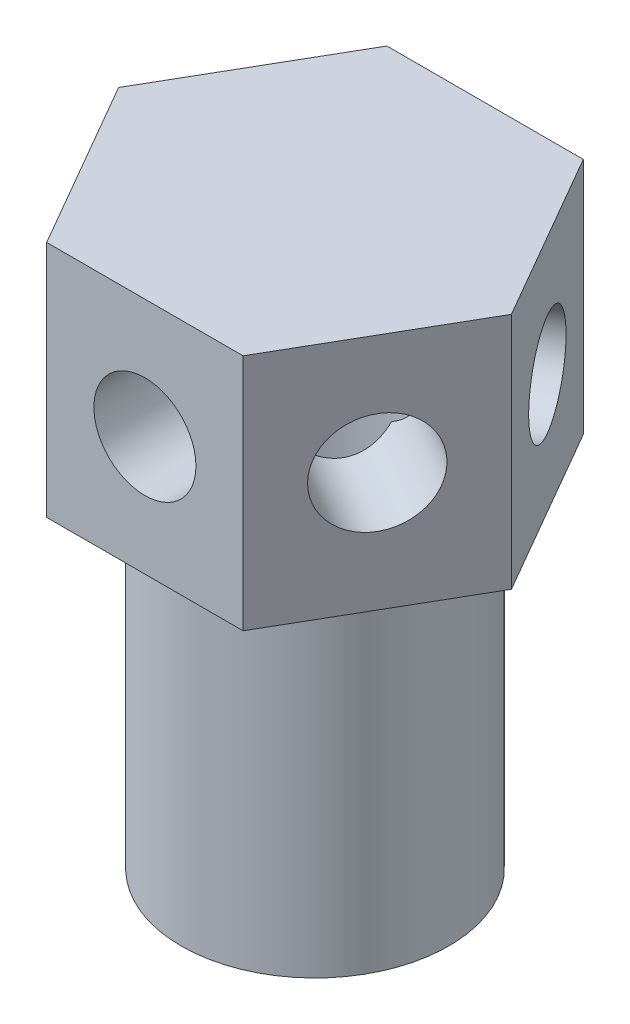
SolidWorks part; units mm, degrees
material "6063-T6"
ref_plane "Ebene vorne" through (0, 0, 0) normal (0, 0, 1) x (1, 0, 0)
ref_plane "Ebene oben" through (0, 0, 0) normal (0, 1, 0) x (1, 0, 0)
ref_plane "Ebene rechts" through (0, 0, 0) normal (1, 0, 0) x (0, 0, -1)
sketch "Skizze1" plane through (0, 0, 0) normal (0, 1, 0) x (1, 0, 0)
  line L1 (2.8868, -5) -> (5.7735, 0)
  line L2 (5.7735, 0) -> (2.8868, 5)
  line L3 (2.8868, 5) -> (-2.8868, 5)
  line L4 (-2.8868, 5) -> (-5.7735, 0)
  line L5 (-5.7735, 0) -> (-2.8868, -5)
  line L6 (-2.8868, -5) -> (2.8868, -5)
  circle A0 centre (0, 0) radius 5 construction
  dimension "D1" = 10
extrude "Aufsatz-Linear austragen1" add sketch "Skizze1" along normal blind 17
sketch "Skizze2" plane through (0, 0, 0) normal (0, -1, 0) x (1, 0, 0)
  circle A0 centre (0, 0) radius 3.935
  circle A1 centre (0, 0) radius 6.935
  dimension "D1" = 3
  dimension "D2" = 7.87
extrude "Schnitt-Linear austragen1" cut sketch "Skizze2" against normal blind 10
sketch "Skizze3" plane through (0, 0, 0) normal (0, -1, 0) x (1, 0, 0)
  circle A0 centre (0, 0) radius 2.25
  dimension "D1" = 4.5
extrude "Schnitt-Linear austragen2" cut sketch "Skizze3" against normal offset from surface (15 mm away) 2 up to face at (0, 17, 0)
sketch "Skizze4" plane through (4.3301, 0, -2.5) normal (0.866, 0, -0.5) x (-0.5, 0, -0.866)
  line L0 (-2.8868, 17) -> (-2.8868, 10) construction
  circle A0 centre (0, 13.5) radius 1.5
  point P5 (-2.8868, 13.5)
  dimension "D1" = 3
extrude "Schnitt-Linear austragen3" cut sketch "Skizze4" against normal through all
pattern_circular "Kreismuster1" count 3 over 240 about axis through (0, 0, 0) along (0, -1, 0) of "Schnitt-Linear austragen3"
